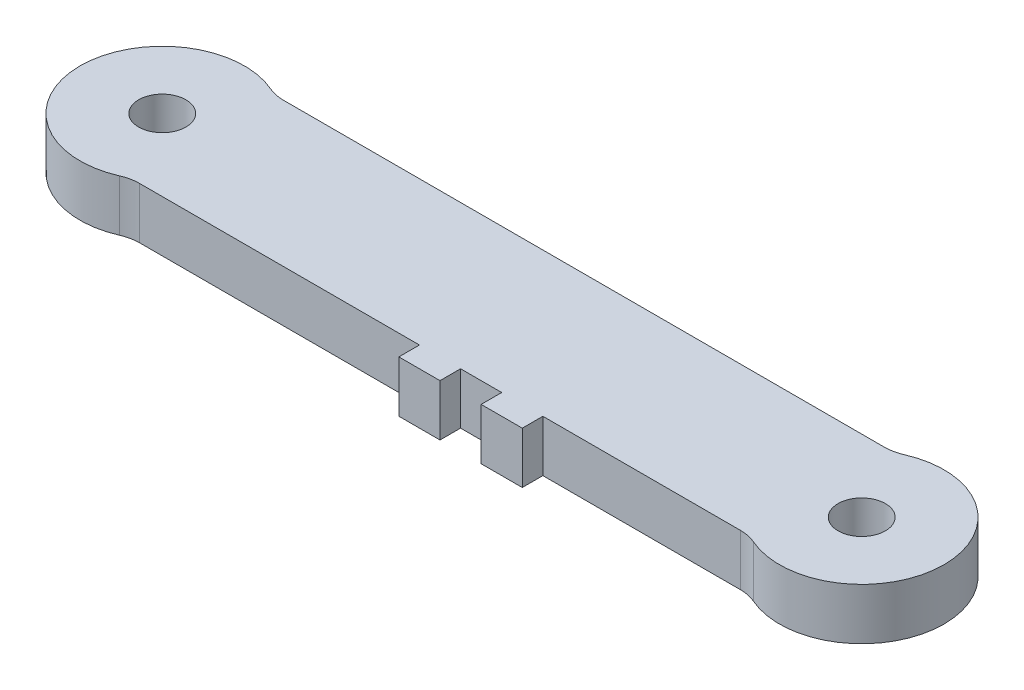
SolidWorks part; units mm, degrees
ref_plane "Front Plane" through (0, 0, 0) normal (0, 0, 1) x (1, 0, 0)
ref_plane "Top Plane" through (0, 0, 0) normal (0, 1, 0) x (1, 0, 0)
ref_plane "Right Plane" through (0, 0, 0) normal (1, 0, 0) x (0, 0, -1)
sketch "Sketch1" plane through (0, 0, 0) normal (0, 1, 0) x (1, 0, 0)
  line L0 (2.4593, 4.445) -> (40.7207, 4.445)
  line L1 (2.4593, -4.445) -> (40.7207, -4.445)
  circle A0 centre (0, 0) radius 1.4605
  circle A1 centre (0, 0) radius 5.08
  circle A2 centre (43.18, 0) radius 1.4605
  circle A3 centre (43.18, 0) radius 5.08
  dimension "D1" = 2.921
  dimension "D2" = 10.16
  dimension "D5" = 2.921
  dimension "D6" = 10.16
  dimension "D3" = 8.89
  dimension "D4" = 4.445
  dimension "D7" = 0
  dimension "D8" = 5.08
  dimension "D9" = 4.445
  dimension "D10" = 43.18
extrude "Boss-Extrude1" add sketch "Sketch1" along normal blind 3.175 contours A1 A0 | A3 L0 A1 L1 | A3 A2
fillet "Fillet1" radius 2.54 4 edges at (2.4593, 1.5875, 4.445) (2.4593, 1.5875, -4.445) (40.7207, 1.5875, -4.445) (40.7207, 1.5875, 4.445)
sketch "Sketch2" plane through (0, 0, 4.445) normal (0, 0, 1) x (1, 0, 0)
  line L0 (3.0454, 3.175) -> (40.1346, 3.175) construction
  line L1 (25.4, 3.175) -> (27.94, 3.175)
  line L2 (25.4, 3.175) -> (25.4, 0)
  line L3 (25.4, 0) -> (27.94, 0)
  line L4 (27.94, 3.175) -> (27.94, 0)
  line L5 (3.0454, 0) -> (40.1346, 0) construction
  line L7 (20.32, 3.175) -> (22.86, 3.175)
  line L8 (20.32, 3.175) -> (20.32, 0)
  line L9 (20.32, 0) -> (22.86, 0)
  line L10 (22.86, 3.175) -> (22.86, 0)
  dimension "D1" = 2.54
  dimension "D2" = 25.4
  dimension "D3" = 2.54
  dimension "D4" = 2.54
extrude "Boss-Extrude2" add sketch "Sketch2" along normal blind 1.27
